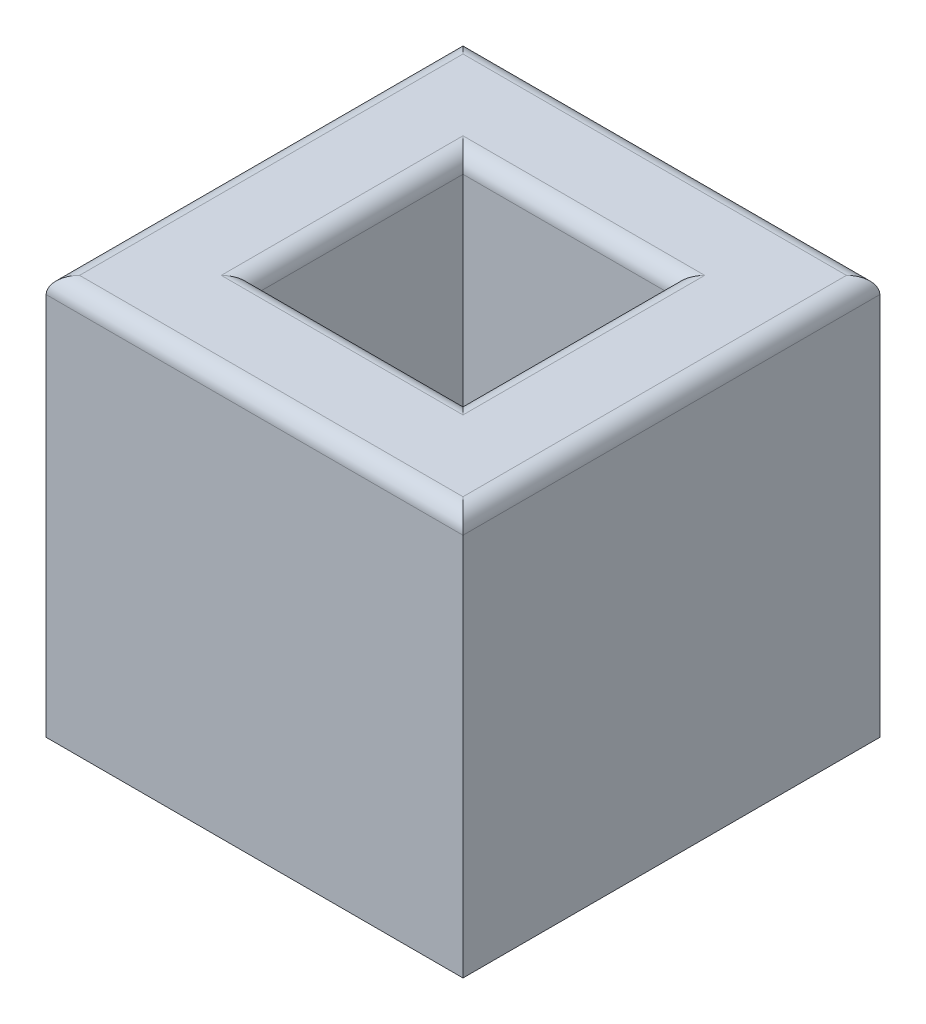
SolidWorks part; units mm, degrees
ref_plane "Front Plane" through (0, 0, 0) normal (0, 0, 1) x (1, 0, 0)
ref_plane "Top Plane" through (0, 0, 0) normal (0, 1, 0) x (1, 0, 0)
ref_plane "Right Plane" through (0, 0, 0) normal (1, 0, 0) x (0, 0, -1)
sketch "Sketch1" plane through (0, 0, 0) normal (0, 1, 0) x (1, 0, 0)
  line L1 (-63.5, -63.5) -> (63.5, -63.5)
  line L2 (-63.5, -63.5) -> (-63.5, 63.5)
  line L3 (-63.5, 63.5) -> (63.5, 63.5)
  line L4 (63.5, -63.5) -> (63.5, 63.5)
  line L5 (-63.5, -63.5) -> (63.5, 63.5) construction
  line L6 (-63.5, 63.5) -> (63.5, -63.5) construction
  point P0 (0, 0)
  dimension "D1" = 127
  dimension "D2" = 127
extrude "Boss-Extrude1" add sketch "Sketch1" along normal blind 127
sketch "Sketch2" plane through (0, 127, 0) normal (0, 1, 0) x (1, 0, 0)
  line L1 (-31.75, -31.75) -> (31.75, -31.75)
  line L2 (-31.75, -31.75) -> (-31.75, 31.75)
  line L3 (-31.75, 31.75) -> (31.75, 31.75)
  line L4 (31.75, -31.75) -> (31.75, 31.75)
  line L5 (-31.75, -31.75) -> (31.75, 31.75) construction
  line L6 (-31.75, 31.75) -> (31.75, -31.75) construction
  point P0 (0, 0)
  dimension "D1" = 63.5
extrude "Cut-Extrude1" cut sketch "Sketch2" against normal through all
chamfer "Chamfer1" distance 5.08 angle 45 8 edges at (0, 0, -63.5) (-63.5, 0, 0) (0, 0, 63.5) (63.5, 0, 0) (0, 0, 31.75) (-31.75, 0, 0) (0, 0, -31.75) (31.75, 0, 0)
fillet "Fillet1" radius 5.08 8 edges at (0, 127, 63.5) (-63.5, 127, 0) (0, 127, -63.5) (63.5, 127, 0) (-31.75, 127, 0) (0, 127, 31.75) (31.75, 127, 0) (0, 127, -31.75)
